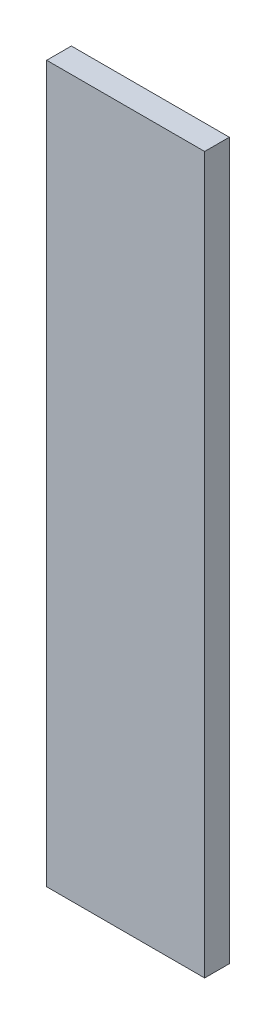
SolidWorks part; units mm, degrees
material "Pine"
ref_plane "Front Plane" through (0, 0, 0) normal (0, 0, 1) x (1, 0, 0)
ref_plane "Top Plane" through (0, 0, 0) normal (0, 1, 0) x (1, 0, 0)
ref_plane "Right Plane" through (0, 0, 0) normal (1, 0, 0) x (0, 0, -1)
sketch "Sketch1" plane through (0, 0, 0) normal (0, 1, 0) x (1, 0, 0)
  line L1 (-48, -7.5) -> (48, -7.5)
  line L2 (-48, -7.5) -> (-48, 7.5)
  line L3 (-48, 7.5) -> (48, 7.5)
  line L4 (48, -7.5) -> (48, 7.5)
  line L5 (-48, -7.5) -> (48, 7.5) construction
  line L6 (-48, 7.5) -> (48, -7.5) construction
  point P0 (0, 0)
  dimension "D1" = 96
  dimension "D2" = 15
extrude "Boss-Extrude1" add sketch "Sketch1" along normal blind 435
